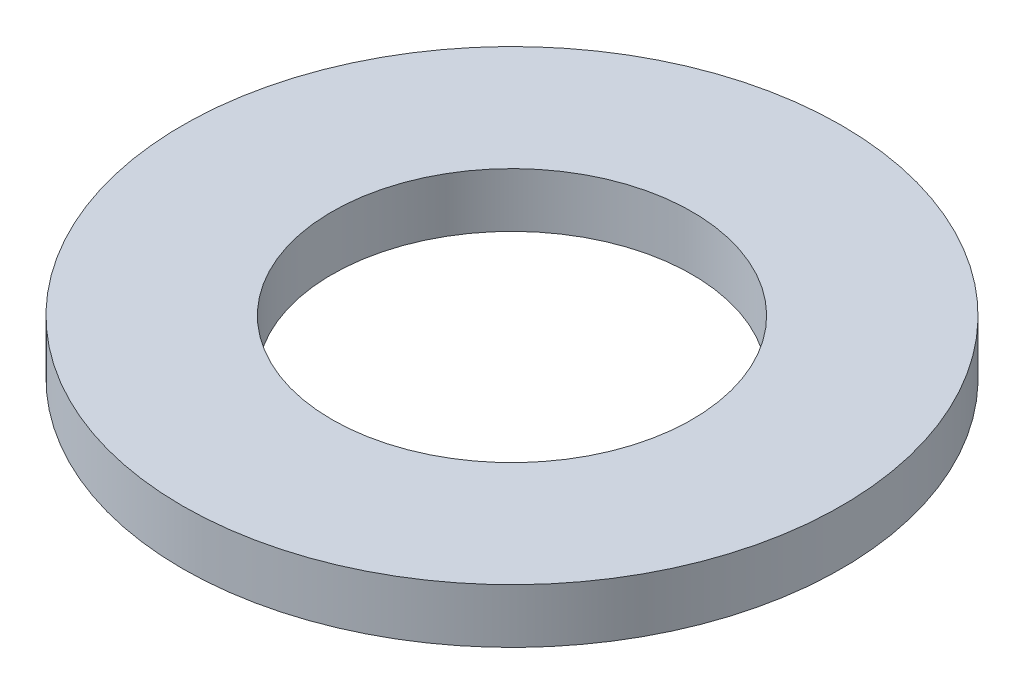
SolidWorks part; units mm, degrees
material "AISI 304"
ref_plane "Front Plane" through (0, 0, 0) normal (0, 0, 1) x (1, 0, 0)
ref_plane "Top Plane" through (0, 0, 0) normal (0, 1, 0) x (1, 0, 0)
ref_plane "Right Plane" through (0, 0, 0) normal (1, 0, 0) x (0, 0, -1)
sketch "Sketch1" plane through (0, 0, 0) normal (0, 1, 0) x (1, 0, 0)
  circle A0 centre (0, 0) radius 2.65
  circle A1 centre (0, 0) radius 4.85
  dimension "D1" = 9.7
  dimension "D2" = 5.3
extrude "Boss-Extrude1" add sketch "Sketch1" along normal blind 0.8
